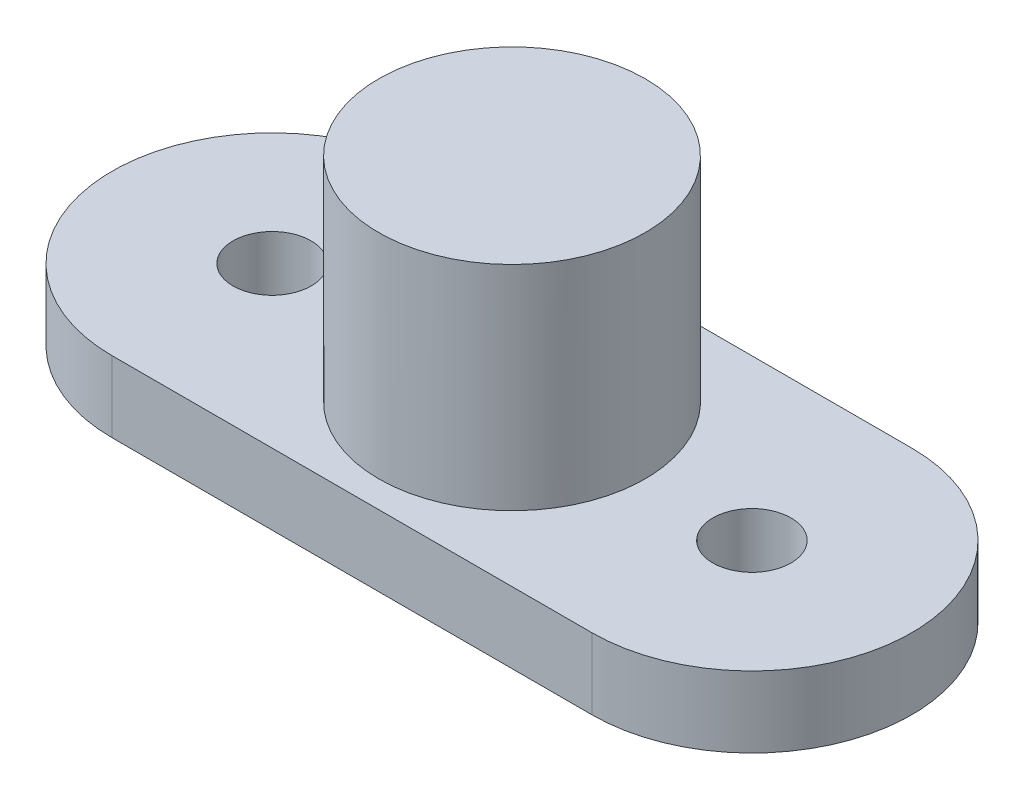
SolidWorks part; units mm, degrees
ref_plane "Front Plane" through (0, 0, 0) normal (0, 0, 1) x (1, 0, 0)
ref_plane "Top Plane" through (0, 0, 0) normal (0, 1, 0) x (1, 0, 0)
ref_plane "Right Plane" through (0, 0, 0) normal (1, 0, 0) x (0, 0, -1)
sketch "Sketch1" plane through (0, 0, 0) normal (0, 1, 0) x (1, 0, 0)
  line L0 (0, 0) -> (6.75, 0)
  line L1 (0, 0) -> (-6.75, 0)
  line L2 (-6.75, 4.4995) -> (6.75, 4.4995)
  line L3 (-6.75, -4.4995) -> (6.75, -4.4995)
  circle A0 centre (-6.75, 0) radius 1.1
  circle A1 centre (6.75, 0) radius 1.1
  arc A2 (6.75, 4.4995) -> (6.75, -4.4995) centre (6.75, 0) cw
  arc A3 (-6.75, 4.4995) -> (-6.75, -4.4995) centre (-6.75, 0) ccw
  circle A6 centre (0, 0) radius 3.75
extrude "Boss-Extrude3" add sketch "Sketch1" along normal blind 2
sketch "Sketch3" plane through (0, 0, 0) normal (0, -1, 0) x (1, 0, 0)
  circle A2 centre (0, 0) radius 3.75
extrude "Boss-Extrude4" add sketch "Sketch3" against normal blind 8
